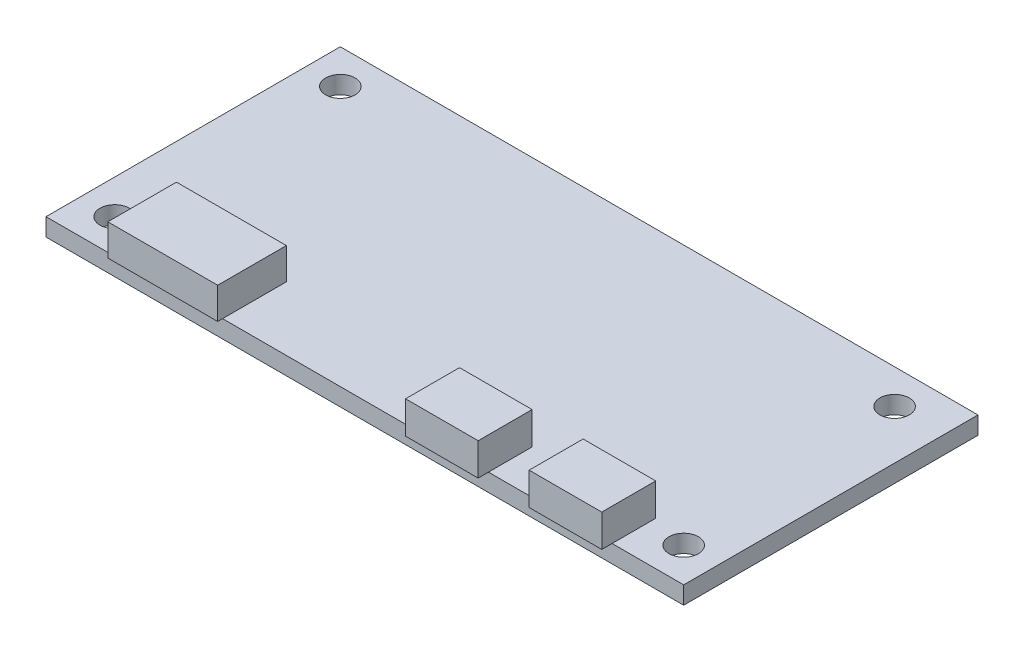
SolidWorks part; units mm, degrees
ref_plane "Front Plane" through (0, 0, 0) normal (0, 0, 1) x (1, 0, 0)
ref_plane "Top Plane" through (0, 0, 0) normal (0, 1, 0) x (1, 0, 0)
ref_plane "Right Plane" through (0, 0, 0) normal (1, 0, 0) x (0, 0, -1)
sketch "Sketch4" plane through (0, 0, 0) normal (0, 1, 0) x (1, 0, 0)
  line L1 (-27.2768, 16.9962) -> (37.7232, 16.9962)
  line L2 (-27.2768, 16.9962) -> (-27.2768, -13.0038)
  line L3 (-27.2768, -13.0038) -> (37.7232, -13.0038)
  line L4 (37.7232, 16.9962) -> (37.7232, -13.0038)
  circle A0 centre (-23.7768, 13.4962) radius 1.5
  circle A1 centre (32.7195, 13.4962) radius 1.5
  circle A2 centre (34.2232, -9.5038) radius 1.5
  circle A3 centre (-23.7768, -9.5038) radius 1.5
  point P12 (5.2232, 16.9962)
  dimension "D7" = 3.5
  dimension "D10" = 3
  dimension "D11" = 3
  dimension "D12" = 3
  dimension "D13" = 3
  dimension "D1" = 65
  dimension "D2" = 30
  dimension "D3" = 23
  dimension "D4" = 3.5
  dimension "D5" = 3.5
  dimension "D6" = 29
  dimension "D8" = 23
  dimension "D9" = 3.5
extrude "Boss-Extrude1" add sketch "Sketch4" against normal blind 1.8 contours A1 | A2 | L2 L1 L4 L3 | A3 | A0
sketch "Sketch5" plane through (0, 0, 0) normal (0, 1, 0) x (1, 0, 0)
  line L0 (-27.2768, 16.9962) -> (-27.2768, -13.0038) construction
  line L1 (-20.4768, -6.5038) -> (-9.2768, -6.5038)
  line L2 (-20.4768, -6.5038) -> (-20.4768, -13.5038)
  line L3 (-20.4768, -13.5038) -> (-9.2768, -13.5038)
  line L4 (-9.2768, -6.5038) -> (-9.2768, -13.5038)
  line L13 (-27.2768, -13.0038) -> (37.7232, -13.0038) construction
  point P6 (-14.8768, -13.5038)
  dimension "D1" = 12.4
  dimension "D2" = 7
  dimension "D3" = 0.5
  dimension "D4" = 11.2
extrude "Boss-Extrude2" add sketch "Sketch5" along normal blind 3.2
sketch "Sketch6" plane through (0, 0, 0) normal (0, 1, 0) x (1, 0, 0)
  line L0 (-27.2768, 16.9962) -> (-27.2768, -13.0038) construction
  line L1 (10.4232, -8.5538) -> (17.8232, -8.5538)
  line L2 (10.4232, -8.5538) -> (10.4232, -14.0538)
  line L3 (10.4232, -14.0538) -> (17.8232, -14.0538)
  line L4 (17.8232, -8.5538) -> (17.8232, -14.0538)
  line L5 (23.0232, -8.5538) -> (30.4232, -8.5538)
  line L6 (23.0232, -8.5538) -> (23.0232, -14.0538)
  line L7 (23.0232, -14.0538) -> (30.4232, -14.0538)
  line L8 (30.4232, -8.5538) -> (30.4232, -14.0538)
  line L9 (-9.2768, -13.0038) -> (37.7232, -13.0038) construction
  point P10 (14.1232, -14.0538)
  point P11 (26.7232, -14.0538)
  point P12 (17.8232, -11.3038)
  point P13 (23.0232, -11.3038)
  dimension "D1" = 41.4
  dimension "D2" = 54
  dimension "D3" = 7.4
  dimension "D4" = 7.4
  dimension "D5" = 5.5
  dimension "D6" = 5.5
  dimension "D7" = 0
  dimension "D8" = 1.05
extrude "Boss-Extrude3" add sketch "Sketch6" along normal blind 3.3
